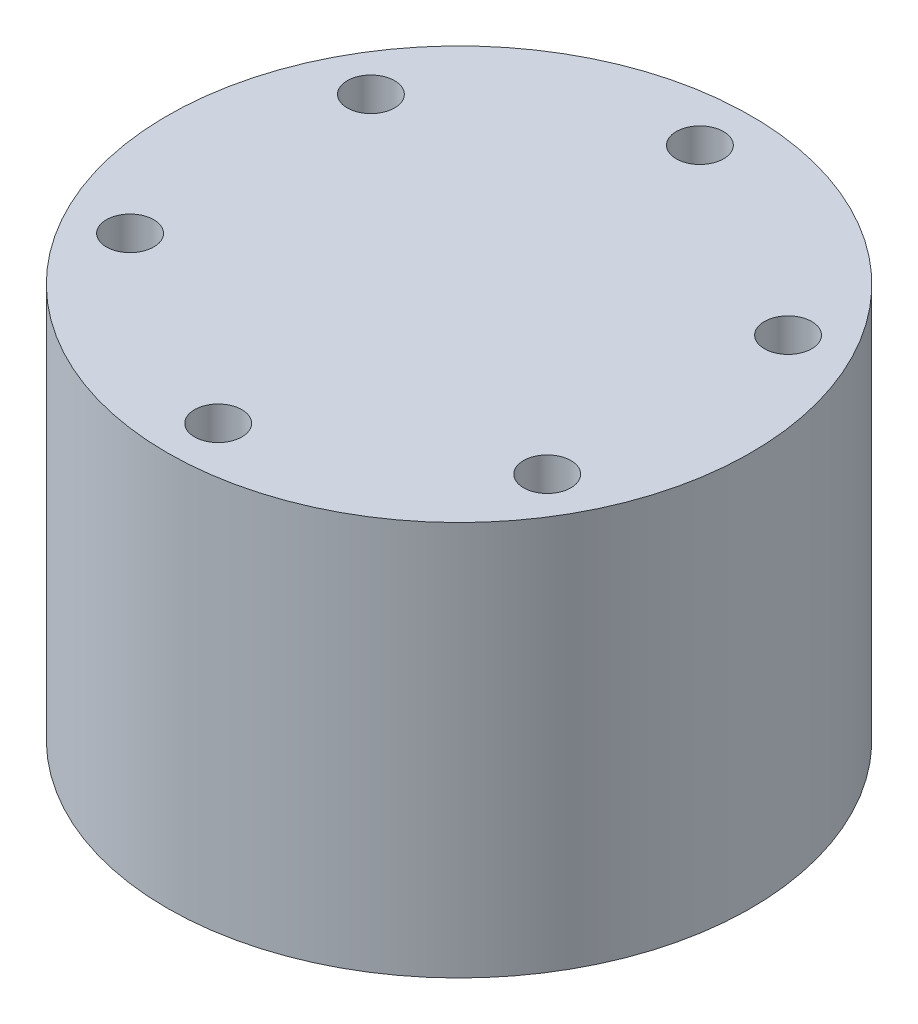
SolidWorks part; units mm, degrees
ref_plane "Front Plane" through (0, 0, 0) normal (0, 0, 1) x (1, 0, 0)
ref_plane "Top Plane" through (0, 0, 0) normal (0, 1, 0) x (1, 0, 0)
ref_plane "Right Plane" through (0, 0, 0) normal (1, 0, 0) x (0, 0, -1)
sketch "Sketch1" plane through (0, 0, 0) normal (0, 1, 0) x (1, 0, 0)
  circle A0 centre (0, 0) radius 18.5
  dimension "D1" = 37
extrude "Boss-Extrude1" add sketch "Sketch1" along normal blind 25
sketch "Sketch2" plane through (0, 25, 0) normal (0, 1, 0) x (1, 0, 0)
  circle A0 centre (0, 0) radius 15.265
  circle A1 centre (0, 15.265) radius 1.5
  circle A2 centre (13.2199, 7.6325) radius 1.5
  circle A3 centre (13.2199, -7.6325) radius 1.5
  circle A4 centre (0, -15.265) radius 1.5
  circle A5 centre (-13.2199, -7.6325) radius 1.5
  circle A6 centre (-13.2199, 7.6325) radius 1.5
  point P18 (0, 0)
  dimension "D1" = 30.53
  dimension "D2" = 3
  dimension "D3" = 6
extrude "Cut-Extrude1" cut sketch "Sketch2" against normal blind 10 contours A0 A1 | A0 A6 | A0 A6 | A0 A1 | A0 A2 | A0 A2 | A0 A3 | A0 A3 | A0 A4 | A0 A4 | A0 A5 | A0 A5
